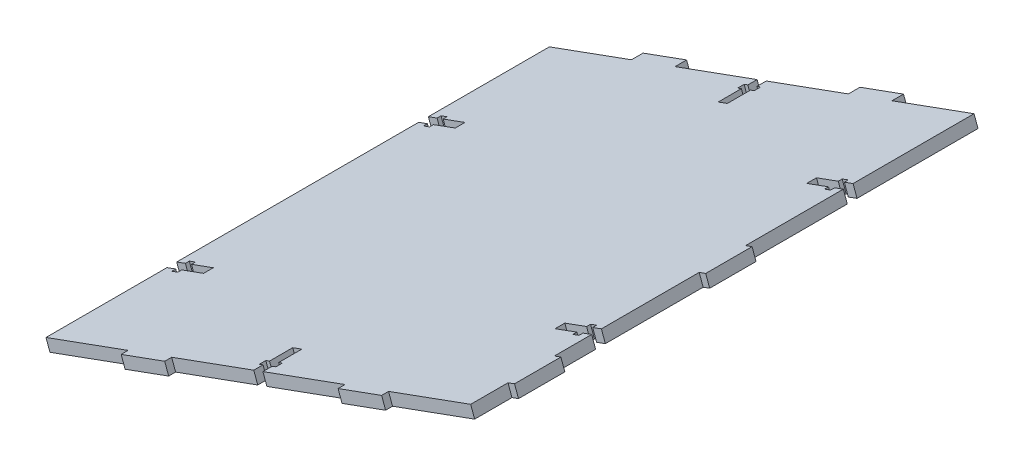
SolidWorks part; units mm, degrees
ref_plane "Front Plane" through (0, 0, 0) normal (0, 0, 1) x (1, 0, 0)
ref_plane "Top Plane" through (0, 0, 0) normal (0, 1, 0) x (1, 0, 0)
ref_plane "Right Plane" through (0, 0, 0) normal (1, 0, 0) x (0, 0, -1)
sketch "Sketch2" plane through (0, 0, 2) normal (0, 0, 1) x (1, 0, 0)
  line L12 (-64.6694, -41.1197) -> (-221.9898, -98.3304) construction
  line L15 (82.6913, -153.7357) -> (61.2307, -94.7225) construction
  line L17 (29.3093, -6.9437) -> (31.0181, -11.6426)
  line L18 (29.3093, -6.9437) -> (-153.9492, -73.587)
  line L19 (31.0181, -11.6426) -> (-152.2404, -78.2859)
  line L20 (-153.9492, -73.587) -> (-152.2404, -78.2859)
  line L24 (-143.2042, -103.1339) -> (-131.9262, -134.1468) construction
  dimension "D1" = 5
extrude "Boss-Extrude1" add sketch "Sketch2" along normal up to surface (217.2 mm away)
sketch "Sketch4" plane through (7.3623, -20.2452, 0) normal (0.3418, -0.9398, 0) x (-0.9398, -0.3418, 0)
  line L0 (70.2286, -2) -> (74.4286, -2)
  line L1 (70.2286, -2) -> (70.2286, -6)
  line L2 (74.4286, -2) -> (74.4286, -6)
  line L3 (68.5286, -6) -> (70.2286, -6)
  line L4 (68.5286, -6) -> (68.5286, -8.8)
  line L5 (76.1286, -6) -> (76.1286, -8.8)
  line L6 (68.5286, -8.8) -> (70.2286, -8.8)
  line L7 (70.2286, -8.8) -> (70.2286, -18.8)
  line L8 (74.4286, -8.8) -> (74.4286, -18.8)
  line L9 (70.2286, -18.8) -> (74.4286, -18.8)
  line L10 (74.4286, -8.8) -> (76.1286, -8.8)
  line L11 (74.4286, -6) -> (76.1286, -6)
  line L14 (-25.1714, -58.4) -> (-25.1714, -54.2)
  line L25 (-25.1714, -2) -> (169.8286, -2) construction
  line L26 (74.4286, -219.2) -> (70.2286, -219.2)
  line L27 (74.4286, -219.2) -> (74.4286, -215.2)
  line L28 (72.3286, -18.8) -> (72.3286, -2) construction
  line L29 (70.2286, -219.2) -> (70.2286, -215.2)
  line L30 (76.1286, -215.2) -> (74.4286, -215.2)
  line L31 (76.1286, -215.2) -> (76.1286, -212.4)
  line L32 (68.5286, -215.2) -> (68.5286, -212.4)
  line L33 (76.1286, -212.4) -> (74.4286, -212.4)
  line L34 (74.4286, -212.4) -> (74.4286, -202.4)
  line L35 (70.2286, -212.4) -> (70.2286, -202.4)
  line L36 (74.4286, -202.4) -> (70.2286, -202.4)
  line L37 (70.2286, -212.4) -> (68.5286, -212.4)
  line L38 (70.2286, -215.2) -> (68.5286, -215.2)
  line L39 (72.3286, -202.4) -> (72.3286, -219.2) construction
  line L40 (-25.1714, -219.2) -> (169.8286, -219.2) construction
  line L41 (-25.1714, -58.4) -> (-21.1714, -58.4)
  line L42 (-25.1714, -54.2) -> (-21.1714, -54.2)
  line L43 (-21.1714, -60.1) -> (-21.1714, -58.4)
  line L44 (-21.1714, -60.1) -> (-18.3714, -60.1)
  line L45 (-21.1714, -52.5) -> (-18.3714, -52.5)
  line L46 (-18.3714, -60.1) -> (-18.3714, -58.4)
  line L47 (-18.3714, -58.4) -> (-8.3714, -58.4)
  line L48 (-18.3714, -54.2) -> (-8.3714, -54.2)
  line L49 (-8.3714, -58.4) -> (-8.3714, -54.2)
  line L50 (-18.3714, -54.2) -> (-18.3714, -52.5)
  line L51 (-21.1714, -54.2) -> (-21.1714, -52.5)
  line L52 (-8.3714, -56.3) -> (-25.1714, -56.3) construction
  line L55 (-25.1714, -219.2) -> (-25.1714, -2) construction
  line L56 (-25.1714, -2) -> (-25.1714, -110.6) construction
  line L57 (-25.1714, -110.6) -> (169.8286, -110.6) construction
  line L58 (-8.3714, -164.9) -> (-25.1714, -164.9) construction
  line L59 (-21.1714, -167) -> (-21.1714, -168.7)
  line L60 (-18.3714, -167) -> (-18.3714, -168.7)
  line L61 (-8.3714, -162.8) -> (-8.3714, -167)
  line L62 (-18.3714, -167) -> (-8.3714, -167)
  line L63 (-18.3714, -162.8) -> (-8.3714, -162.8)
  line L64 (-18.3714, -161.1) -> (-18.3714, -162.8)
  line L65 (-21.1714, -168.7) -> (-18.3714, -168.7)
  line L66 (-21.1714, -161.1) -> (-18.3714, -161.1)
  line L67 (-21.1714, -161.1) -> (-21.1714, -162.8)
  line L68 (-25.1714, -167) -> (-21.1714, -167)
  line L69 (-25.1714, -162.8) -> (-21.1714, -162.8)
  line L70 (-25.1714, -162.8) -> (-25.1714, -167)
  line L76 (169.8286, -219.2) -> (169.8286, -2) construction
  line L77 (72.3286, -171.4513) -> (72.3286, -40.1199) construction
  line L78 (153.0286, -164.9) -> (169.8286, -164.9) construction
  line L87 (169.8286, -2) -> (169.8286, -110.6) construction
  line L88 (153.0286, -56.3) -> (169.8286, -56.3) construction
  line L89 (169.8286, -162.8) -> (169.8286, -167)
  line L90 (169.8286, -162.8) -> (165.8286, -162.8)
  line L91 (169.8286, -167) -> (165.8286, -167)
  line L92 (165.8286, -161.1) -> (165.8286, -162.8)
  line L93 (165.8286, -161.1) -> (163.0286, -161.1)
  line L94 (165.8286, -168.7) -> (163.0286, -168.7)
  line L95 (163.0286, -161.1) -> (163.0286, -162.8)
  line L96 (163.0286, -162.8) -> (153.0286, -162.8)
  line L97 (163.0286, -167) -> (153.0286, -167)
  line L98 (153.0286, -162.8) -> (153.0286, -167)
  line L99 (163.0286, -167) -> (163.0286, -168.7)
  line L100 (165.8286, -167) -> (165.8286, -168.7)
  line L101 (165.8286, -54.2) -> (165.8286, -52.5)
  line L102 (163.0286, -54.2) -> (163.0286, -52.5)
  line L103 (153.0286, -58.4) -> (153.0286, -54.2)
  line L104 (163.0286, -54.2) -> (153.0286, -54.2)
  line L105 (163.0286, -58.4) -> (153.0286, -58.4)
  line L106 (163.0286, -60.1) -> (163.0286, -58.4)
  line L107 (165.8286, -52.5) -> (163.0286, -52.5)
  line L108 (165.8286, -60.1) -> (163.0286, -60.1)
  line L109 (165.8286, -60.1) -> (165.8286, -58.4)
  line L110 (169.8286, -54.2) -> (165.8286, -54.2)
  line L111 (169.8286, -58.4) -> (165.8286, -58.4)
  line L112 (169.8286, -58.4) -> (169.8286, -54.2)
  point P70 (72.3286, -110.6)
  dimension "D1" = 4.2
  dimension "D2" = 1.7
  dimension "D3" = 1.7
  dimension "D4" = 2.8
  dimension "D5" = 10
  dimension "D6" = 4
  dimension "D7" = 4.2
  dimension "D8" = 1.7
  dimension "D9" = 1.7
  dimension "D10" = 2.8
  dimension "D11" = 10
  dimension "D12" = 4
  dimension "D13" = 4.2
  dimension "D14" = 1.7
  dimension "D15" = 1.7
  dimension "D16" = 2.8
  dimension "D17" = 10
  dimension "D18" = 4
extrude "Cut-Extrude3" cut sketch "Sketch4" against normal through all
sketch "Sketch5" plane through (7.3623, -20.2452, 0) normal (0.3418, -0.9398, 0) x (0.9398, 0.3418, 0)
  line L0 (-112.1286, 219.2) -> (-132.1286, 219.2)
  line L1 (-112.1286, 219.2) -> (-112.1286, 222.2)
  line L2 (-132.1286, 219.2) -> (-132.1286, 222.2)
  line L3 (-112.1286, 222.2) -> (-132.1286, 222.2)
  line L4 (-169.8286, 219.2) -> (-74.4286, 219.2) construction
  line L5 (-12.5286, 219.2) -> (-32.5286, 219.2)
  line L6 (-12.5286, 219.2) -> (-12.5286, 222.2)
  line L7 (-32.5286, 219.2) -> (-32.5286, 222.2)
  line L8 (-12.5286, 222.2) -> (-32.5286, 222.2)
  line L9 (-70.2286, 219.2) -> (25.1714, 219.2) construction
  line L10 (25.1714, 100.6) -> (25.1714, 120.6)
  line L11 (25.1714, 100.6) -> (28.1714, 100.6)
  line L12 (25.1714, 120.6) -> (28.1714, 120.6)
  line L13 (28.1714, 100.6) -> (28.1714, 120.6)
  line L14 (25.1714, 58.4) -> (25.1714, 162.8) construction
  line L15 (25.1714, 203.1) -> (25.1714, 183.1)
  line L16 (25.1714, 203.1) -> (28.1714, 203.1)
  line L17 (25.1714, 183.1) -> (28.1714, 183.1)
  line L18 (28.1714, 203.1) -> (28.1714, 183.1)
  line L19 (25.1714, 167) -> (25.1714, 219.2) construction
  line L20 (25.1714, 92.4) -> (25.1714, 128.8)
  line L24 (25.1714, 58.4) -> (25.1714, 162.8) construction
  line L25 (-132.1286, 2) -> (-112.1286, 2)
  line L26 (-132.1286, 2) -> (-132.1286, -3)
  line L27 (-112.1286, 2) -> (-112.1286, -3)
  line L28 (-132.1286, -3) -> (-112.1286, -3)
  line L29 (-169.8286, 2) -> (-74.4286, 2) construction
  line L30 (-32.5286, 2) -> (-12.5286, 2)
  line L31 (-32.5286, 2) -> (-32.5286, -3)
  line L32 (-12.5286, 2) -> (-12.5286, -3)
  line L33 (-32.5286, -3) -> (-12.5286, -3)
  line L34 (-70.2286, 2) -> (25.1714, 2) construction
  line L35 (25.1714, 222.2) -> (-124.8286, 222.2) construction
  point P10 (-122.1286, 219.2)
  point P11 (-22.5286, 219.2)
  point P16 (25.1714, 110.6)
  point P23 (25.1714, 193.1)
  point P31 (25.1714, 110.6)
  point P39 (-122.1286, 2)
  point P49 (-22.5286, 2)
  dimension "D2" = 20
  dimension "D4" = 20
  dimension "D5" = 3
  dimension "D6" = 20
  dimension "D7" = 3
  dimension "D8" = 20
  dimension "D11" = 5
  dimension "D12" = 20
  dimension "D13" = 5
  dimension "D14" = 20
extrude "Boss-Extrude2" add sketch "Sketch5" against normal blind 5 contours L31 L33 L32 L30 | L26 L28 L27 L25 | L11 L13 L12 L10 | L18 L16 L15 L17 | L6 L8 L7 L5 | L1 L3 L2 L0
